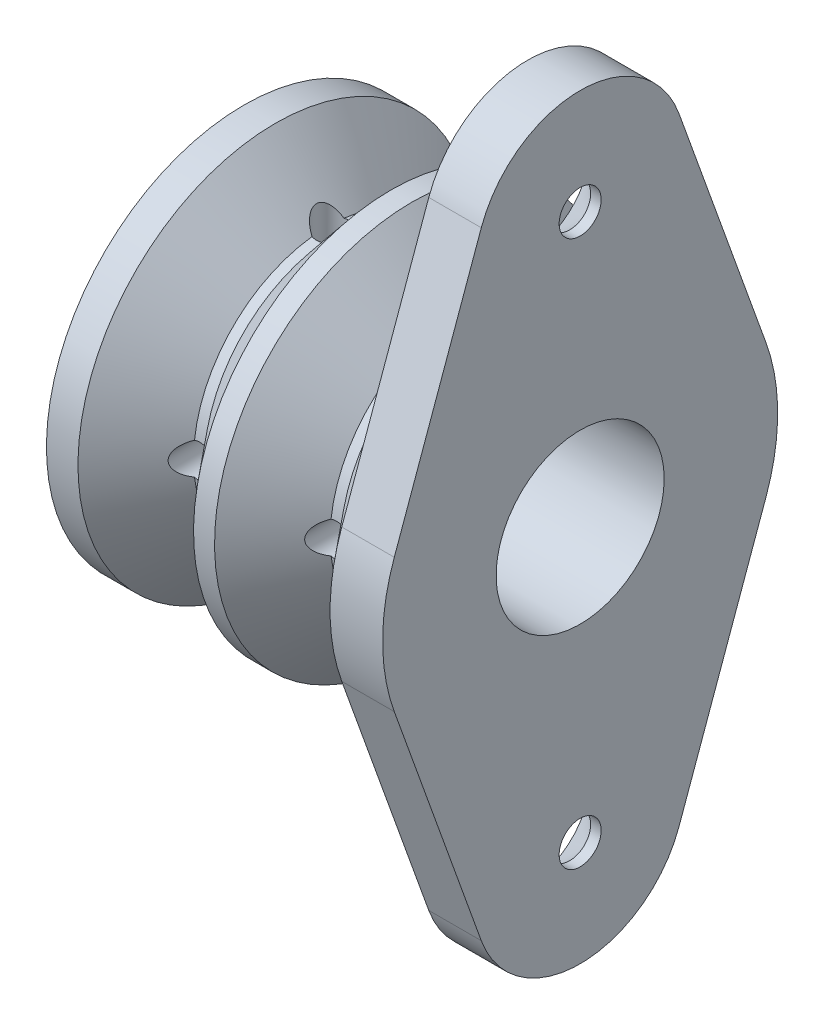
SolidWorks part; units mm, degrees
ref_plane "Front Plane" through (0, 0, 0) normal (0, 0, 1) x (1, 0, 0)
ref_plane "Top Plane" through (0, 0, 0) normal (0, 1, 0) x (1, 0, 0)
ref_plane "Right Plane" through (0, 0, 0) normal (1, 0, 0) x (0, 0, -1)
sketch "Sketch1" plane through (0, 0, 0) normal (0, 0, 1) x (1, 0, 0)
  line L0 (0, 0) -> (0, 9.4)
  line L1 (0, 9.4) -> (0.5, 9.4)
  line L2 (0.5, 9.4) -> (3, 6.4)
  line L3 (3, 6.4) -> (3.5, 6.4)
  line L4 (3.5, 6.4) -> (6, 9.4)
  line L5 (6, 9.4) -> (7.5, 9.4)
  line L6 (7.5, 9.4) -> (7.5, 0)
  line L7 (7.5, 0) -> (0, 0)
  dimension "D1" = 0.5
  dimension "D2" = 1.5
  dimension "D3" = 3
  dimension "D4" = 2.5
  dimension "D5" = 2.5
  dimension "D6" = 0.5
  dimension "D7" = 6.4
revolve "Revolve1" add sketch "Sketch1" angle 360 about L7
mirror "Mirror1" about plane through (0, 0, 0) normal (1, 0, 0) of "Revolve1"
sketch "Sketch2" plane through (0, 0, 0) normal (1, 0, 0) x (0, 0, -1)
  circle A0 centre (0, 13) radius 1
  circle A1 centre (0, -13) radius 1
  point P7 (0, 0)
  dimension "D1" = 2
  dimension "D2" = 2
  dimension "D3" = 13
sketch "Sketch4" plane through (0, 0, 0) normal (1, 0, 0) x (0, 0, -1)
  line L0 (-4.7049, 14.6923) -> (-8.8452, 3.1815)
  line L1 (4.7049, 14.6923) -> (8.8452, 3.1815)
  line L2 (4.7049, -14.6923) -> (8.8452, -3.1815)
  line L3 (-4.7049, -14.6923) -> (-8.8452, -3.1815)
  circle A1 centre (0, 0) radius 9.4
  arc A2 (-8.8452, 3.1815) -> (-8.8452, -3.1815) centre (0, 0) ccw
  circle A16 centre (0, 13) radius 5
  arc A17 (4.7049, 14.6923) -> (-4.7049, 14.6923) centre (0, 13) ccw
  arc A18 (8.8452, -3.1815) -> (8.8452, 3.1815) centre (0, 0) ccw
  circle A19 centre (0, -13) radius 5
  arc A20 (-4.7049, -14.6923) -> (4.7049, -14.6923) centre (0, -13) ccw
  circle A21 centre (0, -13) radius 1 construction
  circle A22 centre (0, 13) radius 1 construction
  circle A23 centre (0, -13) radius 1
  circle A24 centre (0, 13) radius 1
  dimension "D1" = 0
  dimension "D2" = 4
  dimension "D3" = 4
ref_plane "Plane1" through (6, 0, 0) normal (1, 0, 0) x (0, 0, -1)
extrude "Boss-Extrude1" add sketch "Sketch4" along normal blind 2.5 from surface at 6 starting at plane "Plane1"
sketch "Sketch6" plane through (0, 0, 0) normal (0, 1, 0) x (1, 0, 0)
  circle A0 centre (-3.25, 0) radius 0.8
  circle A1 centre (3.25, 0) radius 0.8
  point P5 (0, 0)
  dimension "D1" = 1.6
  dimension "D3" = 1.6
  dimension "D2" = 3.25
  dimension "D4" = 3.25
extrude "Cut-Extrude2" cut sketch "Sketch6" along normal through all both and the other way through all
pattern_circular "CirPattern1" count 2 over 90 about axis through (-7.5, 0, 0) along (1, 0, 0) of "Cut-Extrude2"
chamfer "Chamfer1" distance 2 2 edges at (6, 13, -1) (6, -13, -1)
sketch "Sketch7" plane through (0, 0, 0) normal (1, 0, 0) x (0, 0, -1)
  circle A0 centre (0, 0) radius 4
  dimension "D1" = 8
extrude "Cut-Extrude3" cut sketch "Sketch7" against normal through all both and the other way through all
